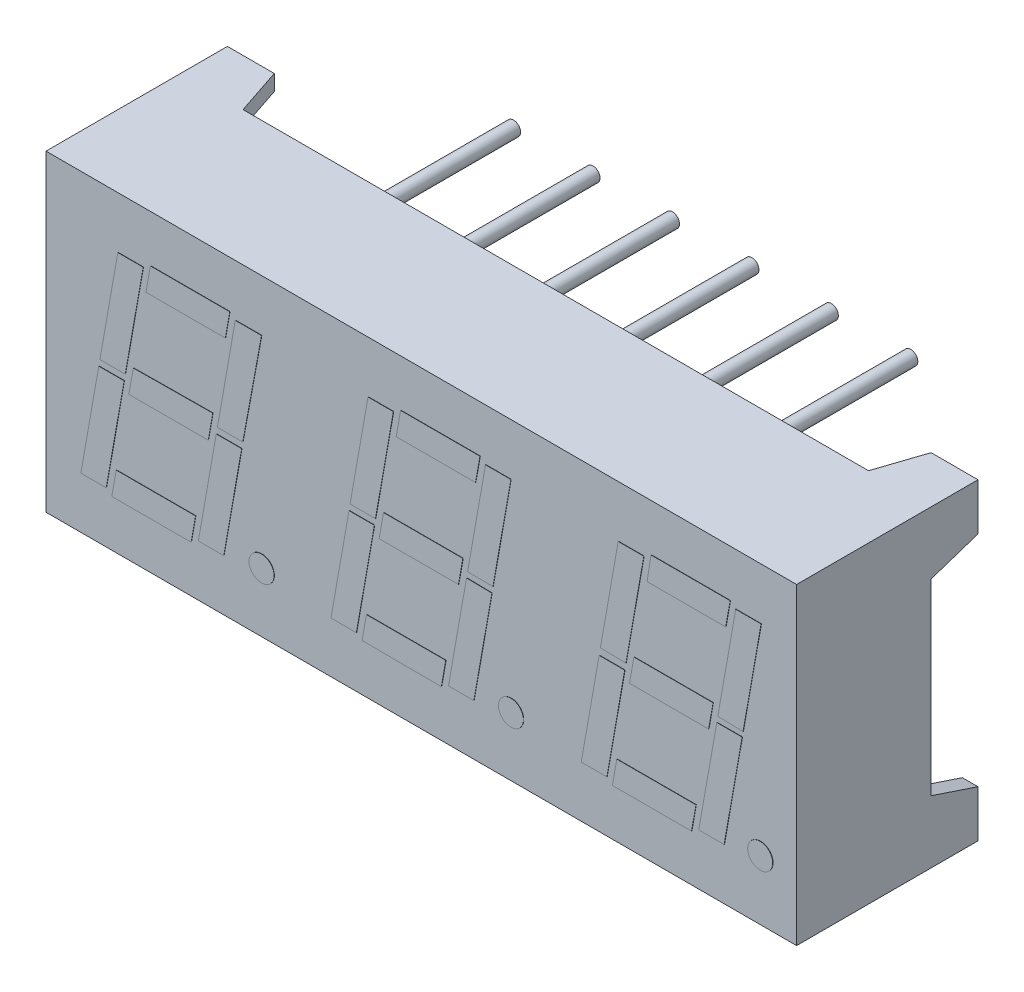
SolidWorks part; units mm, degrees
ref_plane "Спереди" through (0, 0, 0) normal (0, 0, 1) x (1, 0, 0)
ref_plane "Сверху" through (0, 0, 0) normal (0, 1, 0) x (1, 0, 0)
ref_plane "Справа" through (0, 0, 0) normal (1, 0, 0) x (0, 0, -1)
sketch "Эскиз1" plane through (0, 0, 0) normal (0, 0, 1) x (1, 0, 0)
  line L0 (0, 0) -> (-15.2047, 0) construction
  line L1 (12, -5) -> (-12, -5)
  line L2 (12, -5) -> (12, 5)
  line L3 (12, 5) -> (-12, 5)
  line L4 (-12, -5) -> (-12, 5)
  line L5 (12, -5) -> (-12, 5) construction
  line L6 (12, 5) -> (-12, -5) construction
  line L7 (0, 0) -> (0, -8.4862) construction
  point P0 (0, 0)
  dimension "D1" = 10
  dimension "D2" = 24
extrude "Бобышка-Вытянуть1" add sketch "Эскиз1" along normal blind 5.8
sketch "Эскиз4" plane through (0, 0, 5.8) normal (0, 0, 1) x (1, 0, 0)
  line L0 (0, 0) -> (-12, 0) construction
  line L1 (-12.3587, 0.4) -> (15.3834, 0.4) construction
  line L2 (0, 0) -> (0, -5) construction
  line L3 (-12.241, -0.4) -> (-8.6059, -0.4) construction
  line L4 (-4, 11.1862) -> (-4, 10.6416) construction
  line L5 (-4, -5) -> (-4, 8.676) construction
  line L6 (-13.3274, -3.5) -> (-7.6449, -3.5) construction
  line L7 (-3.9759, 8.676) -> (-3.9759, -14.2969) construction
  line L8 (4, 9.357) -> (4, 8.064) construction
  line L9 (4, -9.027) -> (4, 7.7062) construction
  line L10 (-8, 7.5804) -> (-8, -7.9323) construction
  line L11 (8, 5) -> (8, -7.9845) construction
  line L12 (12, 5) -> (-12, 5) construction
  line L13 (-18.3831, 3.5) -> (-10.0892, 3.5) construction
  line L14 (-17.5056, 3.35) -> (-11.7396, 3.35) construction
  line L15 (-20.7827, -3.35) -> (-16.888, -3.35) construction
  line L16 (-8, 0) -> (-7.2402, 4.309) construction
  line L17 (0, 0) -> (1.3065, 7.4093) construction
  line L18 (8, 0) -> (9.3996, 7.9376) construction
  dimension "D1" = 4
  dimension "D2" = 4
  dimension "D3" = 4
  dimension "D4" = 4
  dimension "D5" = 0.4
  dimension "D6" = 0.4
  dimension "D7" = 3.5
  dimension "D8" = 3.5
  dimension "D9" = 0.15
  dimension "D10" = 0.15
sketch "Эскиз5" plane through (0, 0, 5.8) normal (0, 0, 1) x (1, 0, 0)
sketch "Эскиз6" plane through (0, 0, 5.8) normal (0, 0, 1) x (1, 0, 0)
  line L0 (1.0973, 6.2232) -> (-1.1185, 6.6139) construction
  line L1 (-34729.6355, -196961.5506) -> (34730.942, 196968.9599) construction
  line L2 (1.0973, 6.2232) -> (3.3131, 5.8325) construction
  line L3 (-1.1185, 6.6139) -> (-3.4364, -6.5315) construction
  line L4 (3.3131, 5.8325) -> (1.1234, -6.586) construction
  line L5 (-0.3307, 6.475) -> (-2.5604, -6.1704) construction
  line L6 (2.5253, 5.9714) -> (0.3887, -6.1461) construction
  line L8 (-0.3307, 0.1) -> (-3.6245, 0.1) construction
  line L9 (200000, 0) -> (-200012, 0) construction
  line L10 (-15.6427, -0.1) -> (-14.1389, -0.1) construction
  line L12 (2.3023, 0.1) -> (1.49, 0.1)
  line L13 (2.0631, 3.35) -> (2.8754, 3.35)
  line L14 (-200017.5056, 3.35) -> (199988.2604, 3.35) construction
  line L15 (-200018.3831, 3.5) -> (199989.9108, 3.5) construction
  line L16 (2.8754, 3.35) -> (2.3023, 0.1)
  line L17 (-0.3254, 5.3531) -> (-2.4187, -6.5187) construction
  line L18 (0, -7.1985) -> (2.506, 7.0136) construction
  line L19 (0, 200000) -> (0, -200005) construction
  line L20 (3.5383, -2.7) -> (-6.6489, -2.7) construction
  line L21 (-200013.3274, -3.5) -> (199992.3551, -3.5) construction
  line L22 (-14.0616, 2.7) -> (14.1332, 2.7) construction
  line L23 (-1.7454, -2.7) -> (-1.8841, -3.487)
  line L24 (-1.8841, -3.487) -> (0.6521, -3.5)
  line L25 (0.6521, -3.5) -> (0.7932, -2.7)
  line L26 (0.7932, -2.7) -> (-1.7454, -2.7)
  line L27 (1.457, -0.0873) -> (0.8792, -3.364)
  line L28 (0.8792, -3.364) -> (1.6915, -3.364)
  line L29 (1.6915, -3.364) -> (2.2671, -0.1)
  line L30 (2.2671, -0.1) -> (1.457, -0.0873)
  line L31 (-2.0655, -3.364) -> (-2.8779, -3.364)
  line L32 (-2.8779, -3.364) -> (-2.3023, -0.1)
  line L33 (-2.3023, -0.1) -> (-1.49, -0.1)
  line L34 (-1.49, -0.1) -> (-2.0655, -3.364)
  line L35 (2.0631, 3.35) -> (1.49, 0.1)
  line L36 (-0.6521, 3.5) -> (-0.7932, 2.7)
  line L37 (-0.7932, 2.7) -> (1.7454, 2.7)
  line L38 (1.7454, 2.7) -> (1.8864, 3.5)
  line L39 (1.8864, 3.5) -> (-0.6521, 3.5)
  line L40 (-0.8817, 3.35) -> (-1.694, 3.35)
  line L41 (-1.694, 3.35) -> (-2.2671, 0.1)
  line L42 (-2.2671, 0.1) -> (-1.4547, 0.1)
  line L43 (-1.4547, 0.1) -> (-0.8817, 3.35)
  line L44 (-1.1992, 0.3975) -> (-1.339, -0.3953)
  line L45 (-1.339, -0.3953) -> (1.1996, -0.3953)
  line L46 (1.1996, -0.3953) -> (1.3394, 0.3975)
  line L47 (1.3394, 0.3975) -> (-1.1992, 0.3975)
  dimension "D1" = 0.8
  dimension "D2" = 0.8
  dimension "D3" = 0.1
  dimension "D4" = 0.1
  dimension "D5" = 0.2
  dimension "D6" = 0.2
  dimension "D7" = 0.8
  dimension "D8" = 0.8
extrude "Бобышка-Вытянуть2" add sketch "Эскиз6" along normal blind 0.01
sketch "Эскиз7" plane through (0, 0, 5.8) normal (0, 0, 1) x (1, 0, 0)
  line L0 (7.3538, 9.2925) -> (4.5643, -6.5275) construction
  line L1 (-34721.6355, -196961.5506) -> (34739.0351, 196969.4882) construction
  line L2 (11.7258, 8.173) -> (9.0527, -6.9872) construction
  line L3 (2.8754, 3.35) -> (2.8754, -5.1954) construction
  circle A0 centre (2.8754, -3.1073) radius 0.4
  dimension "D1" = 2.25
  dimension "D2" = 2.25
extrude "Бобышка-Вытянуть3" add sketch "Эскиз7" along normal blind 0.01
sketch "Эскиз8" plane through (0, 0, 5.8) normal (0, 0, 1) x (1, 0, 0)
  line L0 (6.7501, 5.8685) -> (4.7227, -5.6291) construction
  line L1 (-34721.6355, -196961.5506) -> (34739.0351, 196969.4882) construction
  line L2 (11.3862, 6.247) -> (9.2122, -6.0823) construction
  line L3 (7.5693, 5.866) -> (5.4621, -6.0846) construction
  line L4 (10.4766, 5.6954) -> (8.4145, -5.9997) construction
  line L5 (1.5191, 2.7) -> (12.6328, 2.7) construction
  line L6 (7.2283, 2.7) -> (7.3552, 3.5)
  line L7 (0.4502, -2.7) -> (12.397, -2.7) construction
  line L8 (-200018.3831, 3.5) -> (199989.9108, 3.5) construction
  line L9 (7.3552, 3.5) -> (9.8864, 3.5)
  line L10 (2.1142, 0.1) -> (12.0901, 0.1) construction
  line L11 (1.457, -0.0873) -> (12.27, -0.0873) construction
  line L12 (5.8062, -5.2847) -> (7.3879, 3.6853) construction
  line L13 (8.3531, -5.1961) -> (9.923, 3.7074) construction
  line L14 (9.8864, 3.5) -> (9.7454, 2.7)
  line L15 (9.7454, 2.7) -> (7.2283, 2.7)
  line L16 (6.8086, 0.4) -> (6.6677, -0.3988)
  line L17 (-200012.3587, 0.4) -> (200015.3834, 0.4) construction
  line L18 (6.6677, -0.3988) -> (9.199, -0.3988)
  line L19 (9.199, -0.3988) -> (9.3398, 0.4)
  line L20 (9.3398, 0.4) -> (6.8086, 0.4)
  line L21 (6.5526, 0.1) -> (5.7364, 0.1197)
  line L22 (5.7364, 0.1197) -> (6.306, 3.35)
  line L23 (-200017.5056, 3.35) -> (199988.2604, 3.35) construction
  line L24 (6.306, 3.35) -> (7.1257, 3.35)
  line L25 (7.1257, 3.35) -> (6.5526, 0.1)
  line L26 (10.0631, 3.35) -> (10.8754, 3.35)
  line L27 (10.8754, 3.35) -> (10.2992, 0.0824)
  line L28 (10.2992, 0.0824) -> (9.49, 0.1)
  line L29 (9.49, 0.1) -> (10.0631, 3.35)
  line L30 (10.2693, -0.0873) -> (9.457, -0.0873)
  line L31 (9.457, -0.0873) -> (8.8817, -3.35)
  line L32 (-200020.7827, -3.35) -> (199983.112, -3.35) construction
  line L33 (8.8817, -3.35) -> (9.694, -3.35)
  line L34 (9.694, -3.35) -> (10.2693, -0.0873)
  line L35 (8.6521, -3.5) -> (8.7932, -2.7)
  line L36 (-200013.3274, -3.5) -> (199992.3551, -3.5) construction
  line L37 (8.7932, -2.7) -> (6.262, -2.7)
  line L38 (6.262, -2.7) -> (6.1209, -3.5)
  line L39 (6.1209, -3.5) -> (8.6521, -3.5)
  line L40 (5.9443, -3.35) -> (5.1246, -3.35)
  line L41 (5.1246, -3.35) -> (5.696, -0.1093)
  line L42 (5.696, -0.1093) -> (6.5157, -0.1093)
  line L43 (6.5157, -0.1093) -> (5.9443, -3.35)
  line L44 (5.9443, -3.35) -> (5.9249, -3.3234)
  dimension "D1" = 2.25
  dimension "D2" = 2.25
  dimension "D3" = 0.2
  dimension "D4" = 0.8
  dimension "D5" = 0.2
extrude "Бобышка-Вытянуть4" add sketch "Эскиз8" along normal blind 0.01
sketch "Эскиз11" plane through (0, 0, 5.8) normal (0, 0, 1) x (1, 0, 0)
  line L0 (10.8467, 3.1874) -> (10.8467, -4.8167) construction
  line L1 (10.8754, 3.35) -> (10.2992, 0.0824) construction
  circle A0 centre (10.8467, -3.0836) radius 0.4
extrude "Бобышка-Вытянуть5" add sketch "Эскиз11" along normal blind 0.01
sketch "Эскиз12" plane through (0, 0, 5.8) normal (0, 0, 1) x (1, 0, 0)
  line L0 (-9.1863, 6.2295) -> (-11.2142, -5.2716) construction
  line L1 (-34737.6355, -196961.5506) -> (34722.3953, 196965.8596) construction
  line L2 (-8.3466, 6.3844) -> (-10.461, -5.6069) construction
  line L3 (-10.8754, -3.35) -> (-10.0631, -3.35)
  line L4 (-8.1361, 6.4268) -> (-10.2163, -5.3711) construction
  line L5 (-5.6322, 6.23) -> (-7.6805, -5.3864) construction
  line L6 (-5.4256, 6.2499) -> (-7.4503, -5.2328) construction
  line L7 (-4.6128, 6.2525) -> (-6.6375, -5.2303) construction
  line L8 (-11.0101, -2.7) -> (-5.1406, -2.7) construction
  line L9 (-200013.3274, -3.5) -> (199992.3551, -3.5) construction
  line L10 (-11.0101, 2.7) -> (-3.8287, 2.7) construction
  line L11 (-200018.3831, 3.5) -> (199989.9108, 3.5) construction
  line L12 (-5.0981, 3.5) -> (-5.0981, -5.7673) construction
  line L13 (-7.3479, -3.5) -> (-7.2068, -2.7)
  line L14 (-7.2068, -2.7) -> (-9.7454, -2.7)
  line L15 (-9.7454, -2.7) -> (-9.8864, -3.5)
  line L16 (-9.8864, -3.5) -> (-7.3479, -3.5)
  line L17 (-200020.7827, -3.35) -> (199983.112, -3.35) construction
  line L18 (-10.7386, 0.1) -> (-4.4693, 0.1) construction
  line L19 (-4.4693, -0.1) -> (-10.7386, -0.1) construction
  line L20 (200000, 0) -> (-200012, 0) construction
  line L21 (-10.0631, -3.35) -> (-9.49, -0.1)
  line L22 (-9.49, -0.1) -> (-10.3023, -0.1)
  line L23 (-10.3023, -0.1) -> (-10.8754, -3.35)
  line L24 (-7.1183, -3.35) -> (-6.5453, -0.1)
  line L25 (-6.5453, -0.1) -> (-5.7329, -0.1)
  line L26 (-5.7329, -0.1) -> (-6.306, -3.35)
  line L27 (-6.306, -3.35) -> (-7.1183, -3.35)
  line L28 (-6.8012, -0.4) -> (-6.6563, 0.4218)
  line L29 (-200012.241, -0.4) -> (199991.3941, -0.4) construction
  line L30 (-6.6563, 0.4218) -> (-9.1988, 0.4)
  line L31 (-200012.3587, 0.4) -> (200015.3834, 0.4) construction
  line L32 (-9.1988, 0.4) -> (-9.3398, -0.4)
  line L33 (-9.3398, -0.4) -> (-6.8012, -0.4)
  line L34 (-9.4547, 0.1) -> (-10.2671, 0.1)
  line L35 (-10.2671, 0.1) -> (-9.694, 3.35)
  line L36 (-200017.5056, 3.35) -> (199988.2604, 3.35) construction
  line L37 (-9.694, 3.35) -> (-8.8817, 3.35)
  line L38 (-8.8817, 3.35) -> (-9.4547, 0.1)
  line L39 (-8.6521, 3.5) -> (-8.7932, 2.7)
  line L40 (-8.7932, 2.7) -> (-6.2546, 2.7)
  line L41 (-6.2546, 2.7) -> (-6.1136, 3.5)
  line L42 (-6.1136, 3.5) -> (-8.6521, 3.5)
  line L43 (-5.9369, 3.35) -> (-5.0981, 3.35)
  line L44 (-5.0981, 3.35) -> (-5.6977, 0.1)
  line L45 (-5.6977, 0.1) -> (-6.51, 0.1)
  line L46 (-6.51, 0.1) -> (-5.9369, 3.35)
  circle A0 centre (-5.0981, -3.1006) radius 0.4
  dimension "D9" = 0.1
  dimension "D1" = 2.25
  dimension "D2" = 2.25
  dimension "D3" = 0.8
  dimension "D4" = 0.2
  dimension "D5" = 0.8
  dimension "D6" = 0.2
  dimension "D7" = 0.8
  dimension "D8" = 0.8
  dimension "D10" = 0.1
extrude "Бобышка-Вытянуть6" add sketch "Эскиз12" along normal blind 0.01
sketch "Эскиз13" plane through (0, 0, 0) normal (0, 0, -1) x (-1, 0, 0)
  line L1 (12, 5) -> (-12, 5)
  line L2 (12, 5) -> (12, -5)
  line L3 (12, -5) -> (-12, -5)
  line L4 (-12, 5) -> (-12, -5)
  line L5 (12, 5) -> (-12, -5) construction
  line L6 (12, -5) -> (-12, 5) construction
  point P0 (0, 0)
  dimension "D1" = 10
  dimension "D2" = 24
extrude "Вырез-Вытянуть5" cut sketch "Эскиз13" against normal blind 1.5
sketch "Эскиз18" plane through (0, 0, 1.5) normal (0, 0, -1) x (-1, 0, 0)
  line L0 (0, 0) -> (-12, 0) construction
  line L2 (-12.5564, 3.81) -> (12.2161, 3.81) construction
  line L3 (12.4657, -3.81) -> (-12.7379, -3.81) construction
  line L4 (0, 0) -> (0, -6.1137) construction
  line L5 (-1.27, 6.4994) -> (-1.27, -5.3878) construction
  line L6 (-3.81, 6.6582) -> (-3.81, -5.66) construction
  line L7 (-6.35, 6.6582) -> (-6.35, -6.454) construction
  line L8 (1.27, 6.6582) -> (1.27, -5.66) construction
  line L9 (3.81, 6.6582) -> (3.81, -5.66) construction
  line L10 (6.35, 6.6582) -> (6.35, -5.6614) construction
  circle A0 centre (-6.35, 3.81) radius 0.225
  circle A1 centre (-3.81, 3.81) radius 0.225
  circle A2 centre (-1.27, 3.81) radius 0.225
  circle A3 centre (1.27, 3.81) radius 0.225
  circle A4 centre (3.81, 3.81) radius 0.225
  circle A5 centre (6.35, 3.81) radius 0.225
  circle A7 centre (-3.81, -3.81) radius 0.225
  circle A8 centre (-1.27, -3.81) radius 0.225
  circle A9 centre (1.27, -3.81) radius 0.225
  circle A10 centre (3.81, -3.81) radius 0.225
  circle A11 centre (6.35, -3.81) radius 0.225
  dimension "D1" = 3.81
  dimension "D2" = 3.81
  dimension "D3" = 1.27
  dimension "D4" = 2.54
  dimension "D5" = 2.54
  dimension "D6" = 1.27
  dimension "D7" = 2.54
  dimension "D8" = 2.54
extrude "Бобышка-Вытянуть7" add sketch "Эскиз18" along normal blind 5
sketch "Эскиз19" plane through (0, 0, 1.5) normal (0, 0, -1) x (-1, 0, 0)
  line L1 (-12, 5) -> (-11.5, 5)
  line L2 (-12, 5) -> (-12, 4.5)
  line L3 (-12, 4.5) -> (-11.5, 4.5)
  line L4 (-11.5, 5) -> (-11.5, 4.5)
  dimension "D1" = 0.5
  dimension "D2" = 0.5
extrude "Бобышка-Вытянуть8" add sketch "Эскиз19" along normal blind 1.5
sketch "Эскиз20" plane through (0, 0, 1.5) normal (0, 0, -1) x (-1, 0, 0)
  line L1 (-12, 4.5) -> (-11.5, 4.5)
  line L2 (-12, 4.5) -> (-12, 3.5)
  line L3 (-12, 3.5) -> (-11.5, 3.5)
  line L4 (-11.5, 4.5) -> (-11.5, 3.5)
  dimension "D1" = 0.5
  dimension "D2" = 1
extrude "Бобышка-Вытянуть9" add sketch "Эскиз20" along normal blind 1.5
sketch "Эскиз21" plane through (0, 0, 1.5) normal (0, 0, -1) x (-1, 0, 0)
  line L1 (-11.5, 5) -> (-10.5, 5)
  line L2 (-11.5, 5) -> (-11.5, 4.5)
  line L3 (-11.5, 4.5) -> (-10.5, 4.5)
  line L4 (-10.5, 5) -> (-10.5, 4.5)
  dimension "D1" = 1
  dimension "D2" = 0.5
extrude "Бобышка-Вытянуть10" add sketch "Эскиз21" along normal blind 1.5
sketch "Эскиз22" plane through (0, 5, 0) normal (0, 1, 0) x (1, 0, 0)
  line L0 (10.5, 0) -> (10.5, -1.5)
  line L1 (10.5, -1.5) -> (10, -1.5)
  line L2 (-12, -1.5) -> (10.5, -1.5) construction
  line L3 (10, -1.5) -> (10.5, 0)
  dimension "D1" = 0.5
extrude "Бобышка-Вытянуть11" add sketch "Эскиз22" against normal blind 0.5
sketch "Эскиз23" plane through (12, 0, 0) normal (1, 0, 0) x (0, 0, -1)
  line L0 (0, 3.5) -> (-1.5, 3.5)
  line L1 (-1.5, 3.5) -> (-1.5, 3)
  line L2 (-1.5, 3.5) -> (-1.5, -5) construction
  line L3 (-1.5, 3) -> (0, 3.5)
  dimension "D1" = 0.5
extrude "Бобышка-Вытянуть12" add sketch "Эскиз23" against normal blind 0.5
sketch "Эскиз24" plane through (0, 0, 1.5) normal (0, 0, -1) x (-1, 0, 0)
  line L1 (-12, -5) -> (-11.5, -5)
  line L2 (-12, -5) -> (-12, -3.5)
  line L3 (-12, -3.5) -> (-11.5, -3.5)
  line L4 (-11.5, -5) -> (-11.5, -3.5)
  dimension "D1" = 1.5
  dimension "D2" = 0.5
extrude "Бобышка-Вытянуть13" add sketch "Эскиз24" along normal blind 1.5
sketch "Эскиз25" plane through (0, 0, 1.5) normal (0, 0, -1) x (-1, 0, 0)
  line L1 (-11.5, -5) -> (-10.5, -5)
  line L2 (-11.5, -5) -> (-11.5, -4.5)
  line L3 (-11.5, -4.5) -> (-10.5, -4.5)
  line L4 (-10.5, -5) -> (-10.5, -4.5)
  dimension "D1" = 0.5
  dimension "D2" = 1
extrude "Бобышка-Вытянуть14" add sketch "Эскиз25" along normal blind 1.5
sketch "Эскиз26" plane through (0, -5, 0) normal (0, -1, 0) x (1, 0, 0)
  line L0 (10.5, 0) -> (10.5, 1.5)
  line L1 (10.5, 1.5) -> (10, 1.5)
  line L2 (10.5, 1.5) -> (-12, 1.5) construction
  line L3 (10, 1.5) -> (10.5, 0)
  dimension "D1" = 0.5
extrude "Бобышка-Вытянуть15" add sketch "Эскиз26" against normal blind 0.5
sketch "Эскиз27" plane through (12, 0, 0) normal (1, 0, 0) x (0, 0, -1)
  line L0 (0, -3.5) -> (-1.5, -3.5)
  line L1 (-1.5, -3.5) -> (-1.5, -3)
  line L2 (-1.5, 3) -> (-1.5, -3.5) construction
  line L3 (-1.5, -3) -> (0, -3.5)
  dimension "D1" = 0.5
extrude "Бобышка-Вытянуть16" add sketch "Эскиз27" against normal blind 0.5
sketch "Эскиз28" plane through (0, 0, 1.5) normal (0, 0, -1) x (-1, 0, 0)
  line L0 (10.5, -5) -> (10.5, -4.5)
  line L1 (-10, -5) -> (12, -5) construction
  line L2 (10.5, -4.5) -> (11.5, -4.5)
  line L3 (11.5, -4.5) -> (11.5, -3.5)
  line L4 (11.5, -3.5) -> (12, -3.5)
  line L5 (12, -3.5) -> (12, -5)
  line L6 (12, -5) -> (10.5, -5)
  line L7 (12, 3.5) -> (11.5, 3.5)
  line L8 (12, -5) -> (12, 5) construction
  line L9 (11.5, 3.5) -> (11.5, 4.5)
  line L10 (11.5, 4.5) -> (10.5, 4.5)
  line L11 (10.5, 4.5) -> (10.5, 5)
  line L12 (12, 5) -> (-10, 5) construction
  line L13 (10.5, 5) -> (12, 5)
  line L14 (12, 5) -> (12, 3.5)
  dimension "D1" = 0.5
  dimension "D2" = 0.5
  dimension "D3" = 0.5
  dimension "D4" = 0.5
  dimension "D5" = 1
  dimension "D6" = 1
  dimension "D7" = 1
  dimension "D8" = 1
extrude "Бобышка-Вытянуть17" add sketch "Эскиз28" along normal blind 1.5
sketch "Эскиз29" plane through (-12, 0, 0) normal (-1, 0, 0) x (0, 0, 1)
  line L0 (1.5, -3.5) -> (0, -3.5)
  line L1 (0, -3.5) -> (1.5, -3)
  line L2 (1.5, -3.5) -> (1.5, 3.5) construction
  line L3 (1.5, -3) -> (1.5, -3.5)
  line L4 (1.5, 3.5) -> (0, 3.5)
  line L5 (0, 3.5) -> (1.5, 3)
  line L6 (1.5, 3) -> (1.5, 3.5)
  dimension "D1" = 0.5
  dimension "D2" = 0.5
extrude "Бобышка-Вытянуть18" add sketch "Эскиз29" against normal blind 0.5
sketch "Эскиз30" plane through (0, 5, 0) normal (0, 1, 0) x (1, 0, 0)
  line L0 (-10.5, -1.5) -> (-10.5, 0)
  line L1 (-10.5, 0) -> (-10, -1.5)
  line L2 (-10.5, -1.5) -> (10, -1.5) construction
  line L3 (-10, -1.5) -> (-10.5, -1.5)
  dimension "D1" = 0.5
extrude "Бобышка-Вытянуть19" add sketch "Эскиз30" against normal blind 0.5
sketch "Эскиз32" plane through (0, -5, 0) normal (0, -1, 0) x (-1, 0, 0)
  line L0 (10.5, 0) -> (10.5, -1.5)
  line L1 (10.5, -1.5) -> (10, -1.5)
  line L2 (-10, -1.5) -> (10.5, -1.5) construction
  line L3 (10, -1.5) -> (10.5, 0)
  dimension "D1" = 0.5
extrude "Бобышка-Вытянуть20" add sketch "Эскиз32" against normal blind 0.5
sketch "Эскиз33" plane through (0, -5, 0) normal (0, -1, 0) x (1, 0, 0)
  text T0 "GNT-2831BD" font "Arial" height 1.5
extrude "Бобышка-Вытянуть21" add sketch "Эскиз33" along normal blind 0.01
